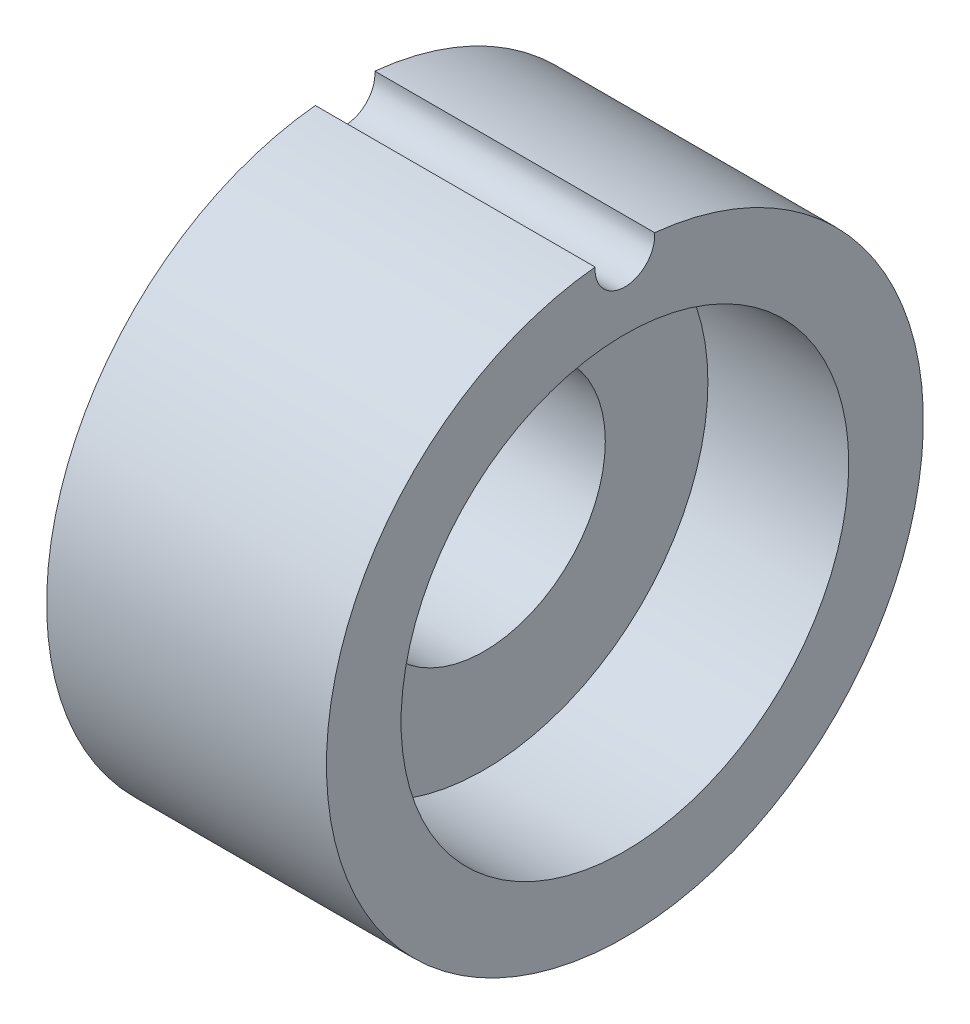
SolidWorks part; units mm, degrees
material "ABS PC"
ref_plane "Front Plane" through (0, 0, 0) normal (0, 0, 1) x (1, 0, 0)
ref_plane "Top Plane" through (0, 0, 0) normal (0, 1, 0) x (1, 0, 0)
ref_plane "Right Plane" through (0, 0, 0) normal (1, 0, 0) x (0, 0, -1)
sketch "Sketch2" plane through (0, 0, 0) normal (1, 0, 0) x (0, 0, -1)
  circle A0 centre (0, 0) radius 8
  circle A1 centre (0, 0) radius 3.25
  dimension "D1" = 16
extrude "Boss-Extrude1" add sketch "Sketch2" along normal blind 7.5
sketch "Sketch3" plane through (7.5, 0, 0) normal (1, 0, 0) x (0, 0, -1)
  circle A0 centre (0, 0) radius 6
extrude "Cut-Extrude1" cut sketch "Sketch3" against normal blind 3.775
sketch "Sketch4" plane through (7.5, 0, 0) normal (1, 0, 0) x (0, 0, -1)
  circle A0 centre (0, 7.9) radius 0.8
  dimension "D1" = 7.9
extrude "Cut-Extrude2" cut sketch "Sketch4" against normal blind 10
